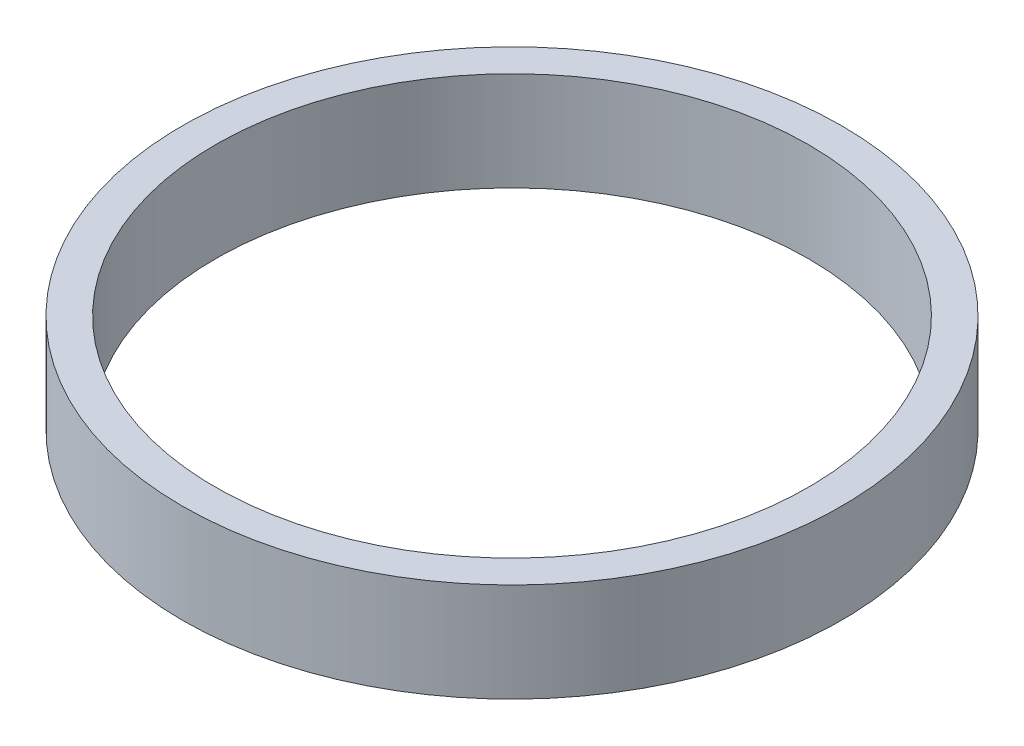
SolidWorks part; units mm, degrees
ref_plane "Front Plane" through (0, 0, 0) normal (0, 0, 1) x (1, 0, 0)
ref_plane "Top Plane" through (0, 0, 0) normal (0, 1, 0) x (1, 0, 0)
ref_plane "Right Plane" through (0, 0, 0) normal (1, 0, 0) x (0, 0, -1)
sketch "Sketch2" plane through (0, 0, 0) normal (0, 0, 1) x (1, 0, 0)
  line L0 (0, -45.6545) -> (0, 54.3455)
  line L1 (0, 0) -> (100, 0)
  line L2 (100, 0) -> (90, 0)
  line L3 (90, 0) -> (90, -15)
  line L4 (90, 0) -> (90, 15)
  line L5 (90, 15) -> (100, 15)
  line L6 (100, 15) -> (100, -15)
  line L7 (100, -15) -> (90, -15)
  dimension "D1" = 100
  dimension "D2" = 100
  dimension "D3" = 15
  dimension "D4" = 15
  dimension "D5" = 10
revolve "Revolve1" add sketch "Sketch2" angle 360 about L0
